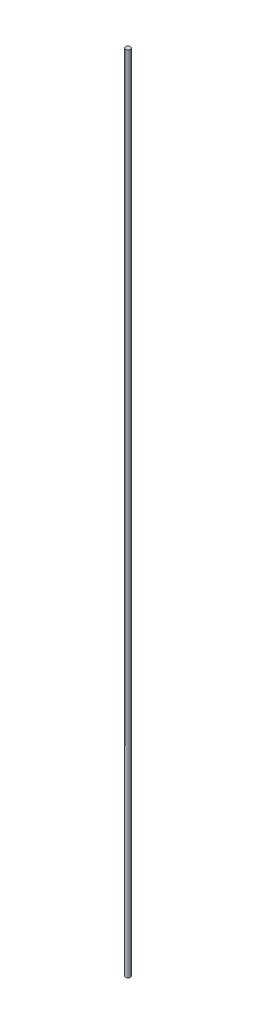
SolidWorks part; units mm, degrees
ref_plane "Front Plane" through (0, 0, 0) normal (0, 0, 1) x (1, 0, 0)
ref_plane "Top Plane" through (0, 0, 0) normal (0, 1, 0) x (1, 0, 0)
ref_plane "Right Plane" through (0, 0, 0) normal (1, 0, 0) x (0, 0, -1)
sketch "Sketch1" plane through (0, 0, 0) normal (0, 1, 0) x (1, 0, 0)
  circle A0 centre (0, 0) radius 3
  dimension "D1" = 6
extrude "Boss-Extrude1" add sketch "Sketch1" along normal blind 1000
